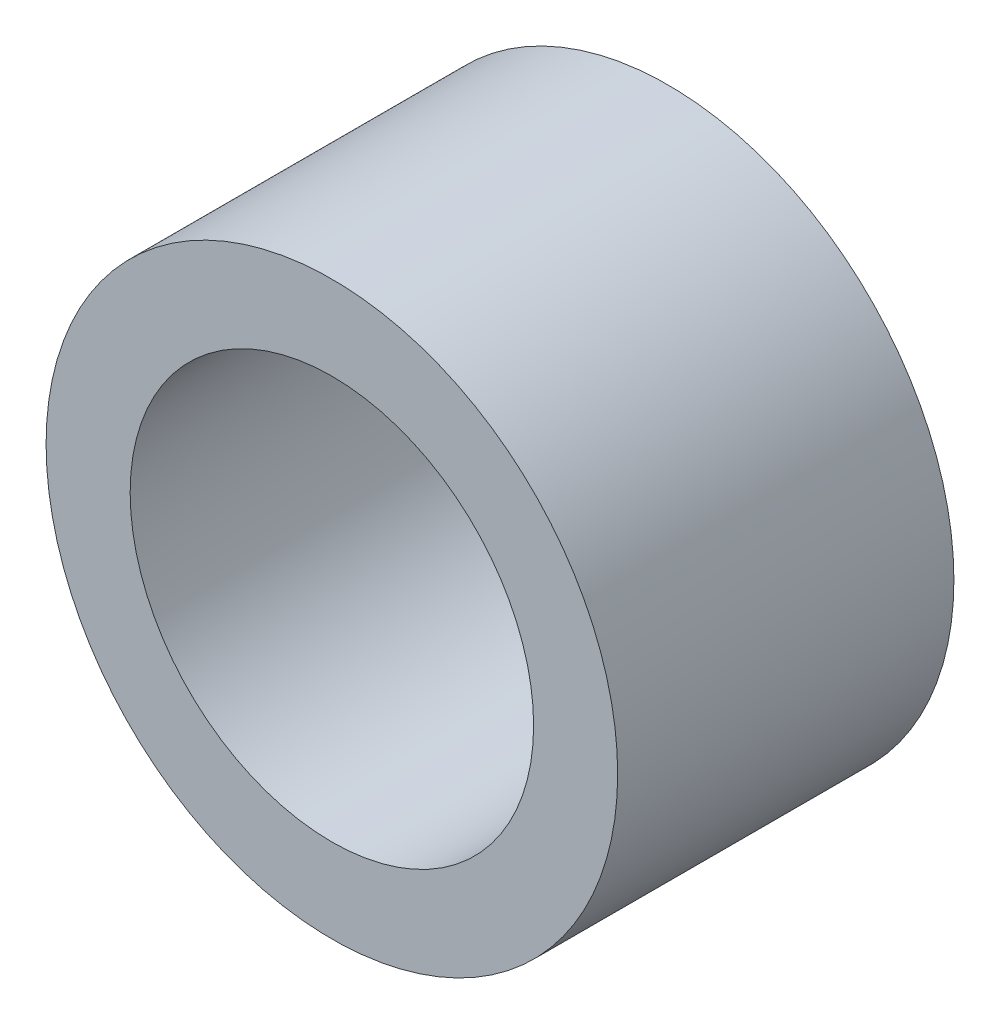
SolidWorks part; units mm, degrees
ref_plane "Front Plane" through (0, 0, 0) normal (0, 0, 1) x (1, 0, 0)
ref_plane "Top Plane" through (0, 0, 0) normal (0, 1, 0) x (1, 0, 0)
ref_plane "Right Plane" through (0, 0, 0) normal (1, 0, 0) x (0, 0, -1)
sketch "Sketch1" plane through (0, 0, 0) normal (0, 0, 1) x (1, 0, 0)
  circle A0 centre (0, 0) radius 12
  circle A1 centre (0, 0) radius 17
  dimension "D1" = 24
  dimension "D2" = 34
extrude "Boss-Extrude1" add sketch "Sketch1" along normal mid plane 20
